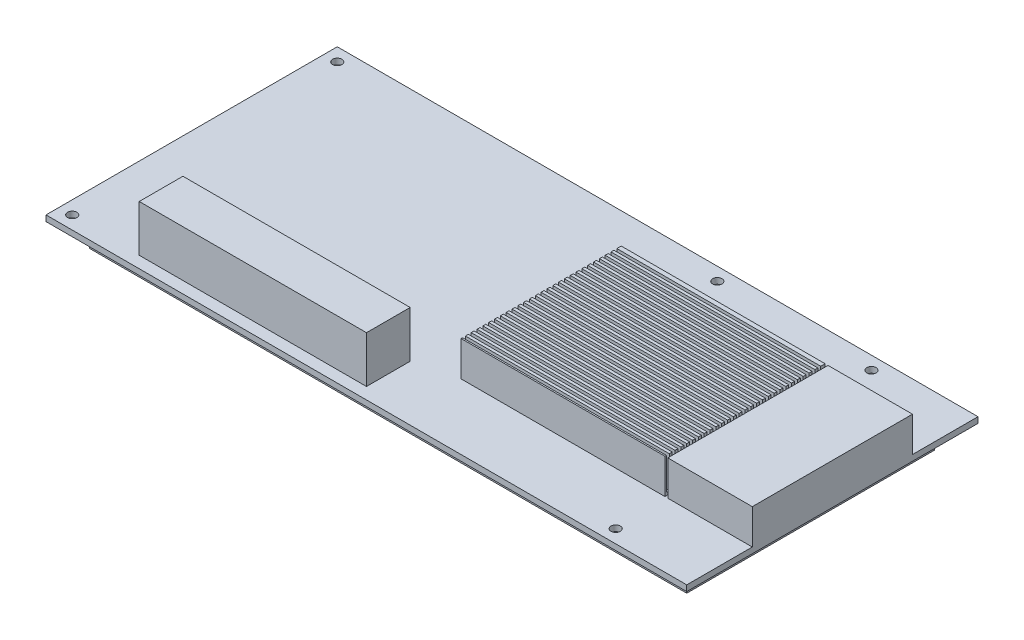
SolidWorks part; units mm, degrees
ref_plane "Front Plane" through (0, 0, 0) normal (0, 0, 1) x (1, 0, 0)
ref_plane "Top Plane" through (0, 0, 0) normal (0, 1, 0) x (1, 0, 0)
ref_plane "Right Plane" through (0, 0, 0) normal (1, 0, 0) x (0, 0, -1)
sketch "Sketch1" plane through (0, 0, 0) normal (0, 1, 0) x (1, 0, 0)
  line L1 (-110, 50) -> (110, 50)
  line L2 (-110, 50) -> (-110, -50)
  line L3 (-110, -50) -> (110, -50)
  line L4 (110, 50) -> (110, -50)
  dimension "D1" = 220
  dimension "D2" = 100
  dimension "D3" = 110
  dimension "D4" = 50
extrude "Boss-Extrude1" add sketch "Sketch1" along normal mid plane 2
sketch "Sketch2" plane through (0, 1, 0) normal (0, 1, 0) x (1, 0, 0)
  line L1 (80, 27.5) -> (10, 27.5)
  line L2 (80, 27.5) -> (80, -27.5)
  line L3 (80, -27.5) -> (10, -27.5)
  line L4 (10, 27.5) -> (10, -27.5)
  line L5 (110, -50) -> (110, 50) construction
  dimension "D1" = 70
  dimension "D2" = 55
  dimension "D3" = 27.5
  dimension "D4" = 30
extrude "Boss-Extrude2" add sketch "Sketch2" along normal blind 12
sketch "Sketch3" plane through (10, 0, 0) normal (-1, 0, 0) x (0, 0, 1)
  line L0 (-27.5, 13) -> (27.5, 13) construction
  line L1 (-26, 13) -> (-25, 13)
  line L2 (-26, 13) -> (-26, 2)
  line L3 (-26, 2) -> (-25, 2)
  line L4 (-25, 13) -> (-25, 2)
  line L5 (-27.5, 13) -> (-27.5, 1) construction
  line L6 (-24, 13) -> (-24, 2)
  line L7 (-24, 2) -> (-23, 2)
  line L8 (-23, 13) -> (-23, 2)
  line L9 (-24, 13) -> (-23, 13)
  line L10 (-22, 13) -> (-22, 2)
  line L11 (-22, 2) -> (-21, 2)
  line L12 (-21, 13) -> (-21, 2)
  line L13 (-22, 13) -> (-21, 13)
  line L14 (-20, 13) -> (-20, 2)
  line L15 (-20, 2) -> (-19, 2)
  line L16 (-19, 13) -> (-19, 2)
  line L17 (-20, 13) -> (-19, 13)
  line L18 (-18, 13) -> (-18, 2)
  line L19 (-18, 2) -> (-17, 2)
  line L20 (-17, 13) -> (-17, 2)
  line L21 (-18, 13) -> (-17, 13)
  line L22 (-16, 13) -> (-16, 2)
  line L23 (-16, 2) -> (-15, 2)
  line L24 (-15, 13) -> (-15, 2)
  line L25 (-16, 13) -> (-15, 13)
  line L26 (-14, 13) -> (-14, 2)
  line L27 (-14, 2) -> (-13, 2)
  line L28 (-13, 13) -> (-13, 2)
  line L29 (-14, 13) -> (-13, 13)
  line L30 (-12, 13) -> (-12, 2)
  line L31 (-12, 2) -> (-11, 2)
  line L32 (-11, 13) -> (-11, 2)
  line L33 (-12, 13) -> (-11, 13)
  line L34 (-10, 13) -> (-10, 2)
  line L35 (-10, 2) -> (-9, 2)
  line L36 (-9, 13) -> (-9, 2)
  line L37 (-10, 13) -> (-9, 13)
  line L38 (-8, 13) -> (-8, 2)
  line L39 (-8, 2) -> (-7, 2)
  line L40 (-7, 13) -> (-7, 2)
  line L41 (-8, 13) -> (-7, 13)
  line L42 (-6, 13) -> (-6, 2)
  line L43 (-6, 2) -> (-5, 2)
  line L44 (-5, 13) -> (-5, 2)
  line L45 (-6, 13) -> (-5, 13)
  line L46 (-4, 13) -> (-4, 2)
  line L47 (-4, 2) -> (-3, 2)
  line L48 (-3, 13) -> (-3, 2)
  line L49 (-4, 13) -> (-3, 13)
  line L50 (-2, 13) -> (-2, 2)
  line L51 (-2, 2) -> (-1, 2)
  line L52 (-1, 13) -> (-1, 2)
  line L53 (-2, 13) -> (-1, 13)
  line L54 (0, 13) -> (0, 2)
  line L55 (0, 2) -> (1, 2)
  line L56 (1, 13) -> (1, 2)
  line L57 (0, 13) -> (1, 13)
  line L58 (2, 13) -> (2, 2)
  line L59 (2, 2) -> (3, 2)
  line L60 (3, 13) -> (3, 2)
  line L61 (2, 13) -> (3, 13)
  line L62 (4, 13) -> (4, 2)
  line L63 (4, 2) -> (5, 2)
  line L64 (5, 13) -> (5, 2)
  line L65 (4, 13) -> (5, 13)
  line L66 (6, 13) -> (6, 2)
  line L67 (6, 2) -> (7, 2)
  line L68 (7, 13) -> (7, 2)
  line L69 (6, 13) -> (7, 13)
  line L70 (8, 13) -> (8, 2)
  line L71 (8, 2) -> (9, 2)
  line L72 (9, 13) -> (9, 2)
  line L73 (8, 13) -> (9, 13)
  line L74 (10, 13) -> (10, 2)
  line L75 (10, 2) -> (11, 2)
  line L76 (11, 13) -> (11, 2)
  line L77 (10, 13) -> (11, 13)
  line L78 (12, 13) -> (12, 2)
  line L79 (12, 2) -> (13, 2)
  line L80 (13, 13) -> (13, 2)
  line L81 (12, 13) -> (13, 13)
  line L82 (14, 13) -> (14, 2)
  line L83 (14, 2) -> (15, 2)
  line L84 (15, 13) -> (15, 2)
  line L85 (14, 13) -> (15, 13)
  line L86 (16, 13) -> (16, 2)
  line L87 (16, 2) -> (17, 2)
  line L88 (17, 13) -> (17, 2)
  line L89 (16, 13) -> (17, 13)
  line L90 (18, 13) -> (18, 2)
  line L91 (18, 2) -> (19, 2)
  line L92 (19, 13) -> (19, 2)
  line L93 (18, 13) -> (19, 13)
  line L94 (20, 13) -> (20, 2)
  line L95 (20, 2) -> (21, 2)
  line L96 (21, 13) -> (21, 2)
  line L97 (20, 13) -> (21, 13)
  line L98 (22, 13) -> (22, 2)
  line L99 (22, 2) -> (23, 2)
  line L100 (23, 13) -> (23, 2)
  line L101 (22, 13) -> (23, 13)
  line L102 (24, 13) -> (24, 2)
  line L103 (24, 2) -> (25, 2)
  line L104 (25, 13) -> (25, 2)
  line L105 (24, 13) -> (25, 13)
  line L106 (26, 13) -> (26, 2)
  line L107 (26, 2) -> (27, 2)
  line L108 (27, 13) -> (27, 2)
  line L109 (26, 13) -> (27, 13)
  line L110 (28, 13) -> (28, 2)
  line L111 (28, 2) -> (29, 2)
  line L112 (29, 13) -> (29, 2)
  line L113 (28, 13) -> (29, 13)
  line L114 (30, 13) -> (30, 2)
  line L115 (30, 2) -> (31, 2)
  line L116 (31, 13) -> (31, 2)
  line L117 (30, 13) -> (31, 13)
  line L118 (32, 13) -> (32, 2)
  line L119 (32, 2) -> (33, 2)
  line L120 (33, 13) -> (33, 2)
  line L121 (32, 13) -> (33, 13)
  dimension "D1" = 1
  dimension "D2" = 1.5
  dimension "D3" = 11
  dimension "D4" = 30
extrude "Cut-Extrude1" cut sketch "Sketch3" against normal through all
sketch "Sketch5" plane through (0, -1, 0) normal (0, -1, 0) x (1, 0, 0)
  line L8 (-102.5, 42.5) -> (-102.5, -42.5)
  line L9 (-102.5, -42.5) -> (102.5, -42.5)
  line L10 (102.5, -42.5) -> (102.5, 42.5)
  line L11 (102.5, 42.5) -> (-102.5, 42.5)
  line L12 (-102.5, 42.5) -> (-102.5, -42.5)
  line L13 (-102.5, -42.5) -> (102.5, -42.5)
  line L14 (102.5, -42.5) -> (102.5, 42.5)
  line L15 (102.5, 42.5) -> (-102.5, 42.5)
  dimension "D1" = 7.5
extrude "Boss-Extrude3" add sketch "Sketch5" along normal blind 8
sketch "Sketch6" plane through (0, -9, 0) normal (0, -1, 0) x (1, 0, 0)
  line L0 (102.5, -42.5) -> (102.5, 42.5) construction
  line L1 (0.5, 22.5) -> (92.5, 22.5)
  line L2 (0.5, 22.5) -> (0.5, -22.5)
  line L3 (0.5, -22.5) -> (92.5, -22.5)
  line L4 (92.5, 22.5) -> (92.5, -22.5)
  dimension "D1" = 92
  dimension "D2" = 45
  dimension "D3" = 22.5
  dimension "D4" = 10
extrude "Boss-Extrude4" add sketch "Sketch6" along normal blind 6
sketch "Sketch7" plane through (0, -9, 0) normal (0, -1, 0) x (1, 0, 0)
  line L0 (46.5, 22.5) -> (46.5, -22.5) construction
  line L1 (92.5, 22.5) -> (0.5, 22.5) construction
  line L2 (0.5, -22.5) -> (92.5, -22.5) construction
  circle A0 centre (-18.5, 0) radius 15
  circle A1 centre (-50.5, 0) radius 15
  circle A2 centre (-18.5, 0) radius 7.5
  circle A3 centre (-50.5, 0) radius 7.5
  dimension "D1" = 30
  dimension "D2" = 65
  dimension "D3" = 32
  dimension "D4" = 7.5
extrude "Boss-Extrude5" add sketch "Sketch7" along normal blind 12 separate body
fillet "Fillet1" radius 1 2 edges at (-18.5, -9, -15) (-18.5, -21, -15)
fillet "Fillet2" radius 1 2 edges at (-50.5, -9, -15) (-50.5, -21, -15)
fillet "Fillet3" radius 1 2 edges at (-50.5, -9, -7.5) (-50.5, -21, -7.5)
fillet "Fillet4" radius 1 2 edges at (-18.5, -9, -7.5) (-18.5, -21, -7.5)
sketch "Sketch9" plane through (0, 1, 0) normal (0, 1, 0) x (1, 0, 0)
  line L0 (110, 50) -> (-110, 50) construction
  line L1 (-110, 50) -> (-110, -50) construction
  line L3 (-110, -50) -> (110, -50) construction
  line L4 (-105.5, 45.5) -> (110, 45.5) construction
  line L5 (110, -50) -> (110, 50) construction
  line L6 (-105.5, -45.5) -> (110, -45.5) construction
  line L7 (110, -50) -> (110, 50) construction
  line L8 (-105.5, 45.5) -> (-105.5, -45.5) construction
  circle A0 centre (-105.5, 45.5) radius 1.6
  circle A1 centre (-105.5, -45.5) radius 1.6
  circle A2 centre (24.99, 45.5) radius 1.6
  circle A3 centre (77.9, 45.5) radius 1.6
  circle A4 centre (165.5, 45.5) radius 1.6
  circle A5 centre (81.1, -45.5) radius 1.6
  circle A6 centre (165.5, -45.5) radius 1.6
  dimension "D5" = 3.2
  dimension "D8" = 275.5
  dimension "D9" = 191.1
  dimension "D10" = 275.5
  dimension "D1" = 4.5
  dimension "D2" = 4.5
  dimension "D3" = 4.5
  dimension "D4" = 4.5
  dimension "D6" = 134.99
  dimension "D7" = 187.9
extrude "Cut-Extrude2" cut sketch "Sketch9" against normal through all
sketch "Sketch10" plane through (0, 1, 0) normal (0, 1, 0) x (1, 0, 0)
  line L0 (-81.9867, -31) -> (-3.9596, -31)
  line L1 (-81.9867, -31) -> (-81.9867, -46)
  line L20 (-3.9596, -31) -> (-3.9596, -46)
  line L24 (106, -46) -> (106, 46)
  line L25 (-106, -46) -> (106, -46)
  line L26 (-106, 46) -> (-106, -46)
  line L27 (106, 46) -> (-106, 46)
  line L29 (-81.9867, -46) -> (-3.9596, -46)
  dimension "D3" = 15
  dimension "D1" = 4
sketch "Sketch12" plane through (0, -9, 0) normal (0, -1, 0) x (1, 0, 0)
  line L0 (110, 50) -> (110, -50) construction
  circle A0 centre (-90, -26.7034) radius 2
  dimension "D1" = 4
  dimension "D2" = 200
extrude "Boss-Extrude10" add sketch "Sketch10" along normal blind 16
sketch "Sketch14" plane through (0, 1, 0) normal (0, 1, 0) x (1, 0, 0)
  line L0 (110, -50) -> (110, 50) construction
  line L1 (81, 27.5) -> (110, 27.5)
  line L2 (81, 27.5) -> (81, -27.5)
  line L3 (81, -27.5) -> (110, -27.5)
  line L4 (110, 27.5) -> (110, -27.5)
  line L5 (80, 27.5) -> (10, 27.5) construction
  line L6 (10, -27.5) -> (80, -27.5) construction
  dimension "D1" = 29
extrude "Boss-Extrude11" add sketch "Sketch14" along normal blind 12 separate body
sketch "Sketch16" plane through (-92.2, -194.35, -4) normal (0, 1, 0) x (-1, 0, 0)
  line L1 (-244.5, 58.5) -> (84.5, 58.5)
  line L2 (-244.5, 58.5) -> (-244.5, -53.5)
  line L3 (-244.5, -53.5) -> (84.5, -53.5)
  line L4 (84.5, 58.5) -> (84.5, -53.5)
  line L5 (-234.5, -45) -> (-234.5, 48) construction
  line L6 (74.5, 48) -> (74.5, -45) construction
  line L7 (50.5, 51) -> (64.5, 51) construction
  line L8 (-202.2, -46) -> (17.8, -46) construction
  dimension "D1" = 10
  dimension "D2" = 10
  dimension "D3" = 7.5
  dimension "D4" = 7.5
sketch "Sketch15" plane through (-92.2, -194.35, -4) normal (0, 0, 1) x (0, 1, 0)
  line L0 (-161.05, 71.5) -> (-161.05, -71.5) construction
  line L1 (-171.05, 84.5) -> (226.35, 84.5)
  line L2 (-171.05, 84.5) -> (-171.05, -244.5)
  line L3 (-171.05, -244.5) -> (226.35, -244.5)
  line L4 (226.35, 84.5) -> (226.35, -244.5)
  line L5 (-2.85, -234.5) -> (-37.15, -234.5) construction
  line L6 (211.35, -10.2133) -> (211.35, -88.2404) construction
  line L7 (-2.85, 74.5) -> (-37.15, 74.5) construction
  dimension "D1" = 10
  dimension "D2" = 10
  dimension "D3" = 15
  dimension "D4" = 10
extrude "Boss-Extrude12" add sketch "Sketch15" along normal up to vertex (58.5 mm away) and the other way up to vertex (53.5 mm away) separate body up to point (152.3, -194.35, 54.5) other way up to point (152.3, -194.35, -57.5)
combine bodies "Combine1" operation type add bodies to combine 107 113 114 106
shell "Shell1" thickness 2
sketch "Sketch18" plane through (0, 0, 56.5) normal (0, 0, 1) x (1, 0, 0)
  circle A0 centre (20, 0) radius 5
  circle A4 centre (40, 0) radius 5
  circle A5 centre (60, 0) radius 5
  circle A6 centre (80, 0) radius 5
  dimension "D1" = 10
  dimension "D2" = 20
  dimension "D3" = 4
extrude "Boss-Extrude13" add sketch "Sketch18" along normal blind 2.5 separate body
sketch "Sketch19" plane through (0, 0, 56.5) normal (0, 0, 1) x (1, 0, 0)
  line L0 (-178.7, 34) -> (-178.7, -367.4) construction
  circle A0 centre (-133.7, 0) radius 2.5
  circle A1 centre (-173.7, 0) radius 2.5
  dimension "D1" = 5
  dimension "D3" = 40
  dimension "D2" = 45
extrude "Boss-Extrude14" add sketch "Sketch19" along normal blind 3 separate body
delete or keep bodies "Body-Delete/Keep 1" type delete bodies bodies 115 117 120 121 122 119 123
